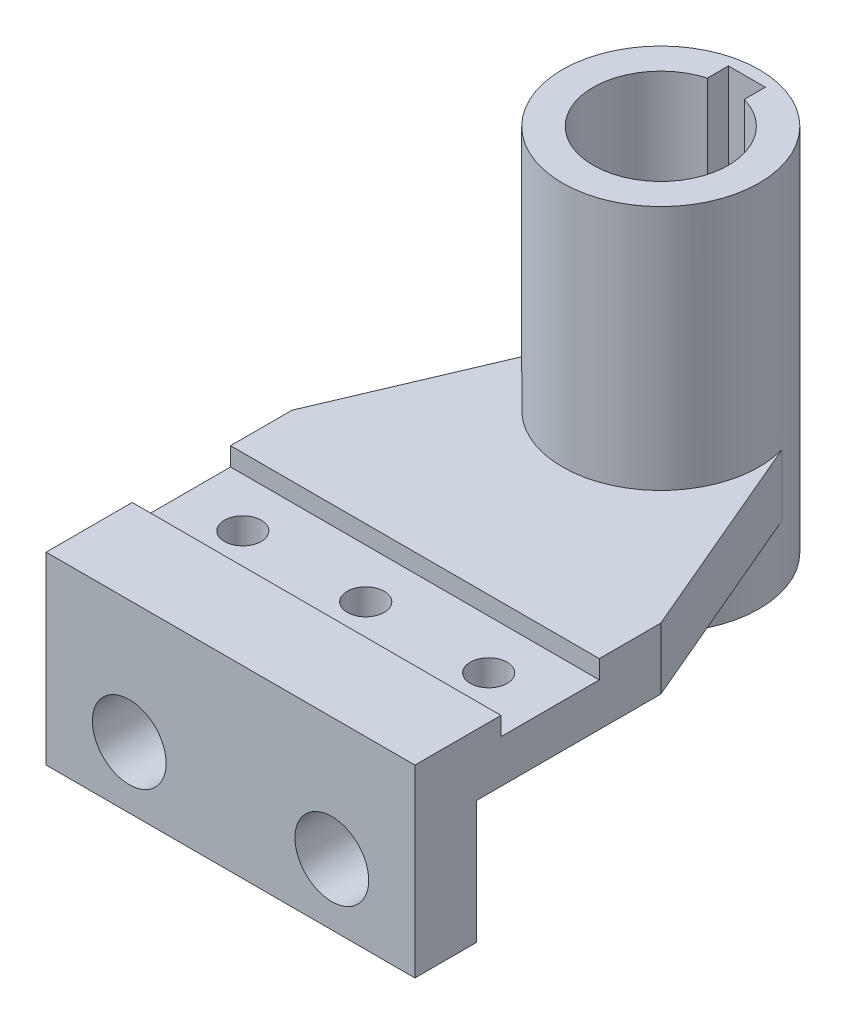
SolidWorks part; units mm, degrees
material "Copper"
ref_plane "Front Plane" through (0, 0, 0) normal (0, 0, 1) x (1, 0, 0)
ref_plane "Top Plane" through (0, 0, 0) normal (0, 1, 0) x (1, 0, 0)
ref_plane "Right Plane" through (0, 0, 0) normal (1, 0, 0) x (0, 0, -1)
sketch "Sketch1" plane through (0, 0, 0) normal (0, 1, 0) x (1, 0, 0)
  line L0 (-30, 0) -> (-15.4114, 34.3)
  line L2 (-30, 0) -> (-30, -40)
  line L3 (-30, -40) -> (30, -40)
  line L4 (30, 0) -> (30, -40)
  line L5 (15.4114, 34.3) -> (30, 0)
  arc A0 (15.4114, 34.3) -> (-15.4114, 34.3) centre (0, 30) ccw
  point P4 (0, -40)
  dimension "D4" = 32
  dimension "D1" = 40
  dimension "D2" = 60
  dimension "D3" = 40
  dimension "D5" = 70
extrude "Boss-Extrude1" add sketch "Sketch1" along normal blind 10
sketch "Sketch2" plane through (0, 10, 0) normal (0, 1, 0) x (1, 0, 0)
  line L5 (-30, 0) -> (-30, -40)
  line L6 (-30, -40) -> (30, -40)
  line L7 (30, -40) -> (30, 0)
  line L8 (30, 0) -> (15.4114, 34.3)
  line L9 (-15.4114, 34.3) -> (-30, 0)
  line L10 (-30, 0) -> (-30, -40)
  line L11 (-30, -40) -> (30, -40)
  line L12 (30, -40) -> (30, 0)
  line L13 (30, 0) -> (15.4114, 34.3)
  line L14 (-15.4114, 34.3) -> (-30, 0)
  circle A0 centre (0, 30) radius 16
  arc A1 (15.4114, 34.3) -> (-15.4114, 34.3) centre (0, 30) ccw
  arc A2 (15.4114, 34.3) -> (-15.4114, 34.3) centre (0, 30) ccw
  arc M11 (15.4114, 34.3) -> (-15.4114, 34.3) centre (0, 30) ccw
  dimension "D2" = 32
  dimension "D1" = 0
extrude "Boss-Extrude2" add sketch "Sketch2" along normal blind 40 and the other way blind 20 contours A0 M11
sketch "Sketch3" plane through (0, 50, 0) normal (0, 1, 0) x (1, 0, 0)
  line L1 (-3, 44) -> (3, 44)
  line L2 (-3, 44) -> (-3, 40.583)
  line L4 (3, 44) -> (3, 40.583)
  line L6 (0, 41) -> (3, 44) construction
  arc A0 (-3, 40.583) -> (3, 40.583) centre (0, 30) ccw
  circle A1 centre (0, 30) radius 16
  circle A2 centre (0, 30) radius 16
  point P1 (0, 41)
  point P9 (0, 19)
  dimension "D2" = 22
  dimension "D3" = 6
  dimension "D4" = 25
  dimension "D1" = 0
extrude "Cut-Extrude1" cut sketch "Sketch3" against normal through all contours L1 L4 A0 L2
ref_plane "Plane1" through (0, 0, 0) normal (0, -1, 0) x (-1, 0, 0)
sketch "Sketch5" plane through (0, 0, 0) normal (0, -1, 0) x (-1, 0, 0)
  line L0 (-30, -30) -> (30, -30)
  line L5 (30, 0) -> (15.4114, 34.3)
  line L6 (-15.4114, 34.3) -> (-30, 0)
  line L7 (-30, 0) -> (-30, -40)
  line L8 (-30, -40) -> (30, -40)
  line L9 (30, -40) -> (30, 0)
  line L12 (-30, -30) -> (-30, -40)
  line L13 (-30, -40) -> (30, -40)
  line L14 (30, -40) -> (30, -30)
  arc A1 (-15.4114, 34.3) -> (15.4114, 34.3) centre (0, 30) ccw
  dimension "D2" = 10
  dimension "D1" = 0
extrude "Boss-Extrude3" add sketch "Sketch5" along normal blind 20
sketch "Sketch6" plane through (0, 0, 40) normal (0, 0, 1) x (1, 0, 0)
  line L4 (-30, 10) -> (-30, -20)
  line L5 (-30, -20) -> (30, -20)
  line L6 (30, -20) -> (30, 10)
  line L7 (30, 10) -> (-30, 10)
  line L8 (-30, 10) -> (-30, -20)
  line L9 (-30, -20) -> (30, -20)
  line L10 (30, -20) -> (30, 10)
  line L11 (30, 10) -> (-30, 10)
  circle A0 centre (-16.4773, -10) radius 6
  circle A1 centre (16.4773, -10) radius 6
  dimension "D2" = 12
  dimension "D3" = 10
  dimension "D4" = 13.5227
  dimension "D1" = 0
extrude "Cut-Extrude2" cut sketch "Sketch6" against normal up to next contours A1 | A0
ref_plane "Plane4" through (0, 10, 0) normal (0, 1, 0) x (1, 0, 0)
sketch "Sketch9" plane through (0, 10, 0) normal (0, 1, 0) x (1, 0, 0)
  line L0 (-30, -10) -> (30, -10)
  line L1 (-30, -26) -> (30, -26)
  line L3 (0, -57.4144) -> (0, -10) construction
  line L4 (0, 0) -> (0, 4.8971) construction
  line L5 (-15.4114, 34.3) -> (-30, 0)
  line L6 (-30, 0) -> (-30, -40)
  line L7 (-30, -40) -> (30, -40)
  line L8 (30, -40) -> (30, 0)
  line L9 (30, 0) -> (15.4114, 34.3)
  line L11 (-30, -10) -> (-30, -26)
  line L13 (30, -26) -> (30, -10)
  line L15 (-30, -18) -> (30, -18) construction
  circle A0 centre (0, -18) radius 3
  arc A1 (-15.4114, 34.3) -> (15.4114, 34.3) centre (0, 30) ccw
  circle A2 centre (20, -18) radius 3
  circle A3 centre (-20, -18) radius 3
  dimension "D4" = 6
  dimension "D2" = 10
  dimension "D3" = 16
  dimension "D1" = 0
  dimension "D5" = 2
extrude "Cut-Extrude4" cut sketch "Sketch9" against normal blind 3 contours A3 | A0 | A2 | L11 L1 L13 L0
ref_plane "Plane5" through (0, 17, 0) normal (0, 1, 0) x (1, 0, 0)
sketch "Sketch10" plane through (0, 17, 0) normal (0, 1, 0) x (1, 0, 0)
  circle A0 centre (20, -18) radius 3 construction
  circle A1 centre (0, -18) radius 3 construction
  circle A2 centre (-20, -18) radius 3 construction
  circle A3 centre (20, -18) radius 3
  circle A4 centre (0, -18) radius 3
  circle A5 centre (-20, -18) radius 3
extrude "Cut-Extrude5" cut sketch "Sketch10" against normal through all contours A5 | A4 | A3
